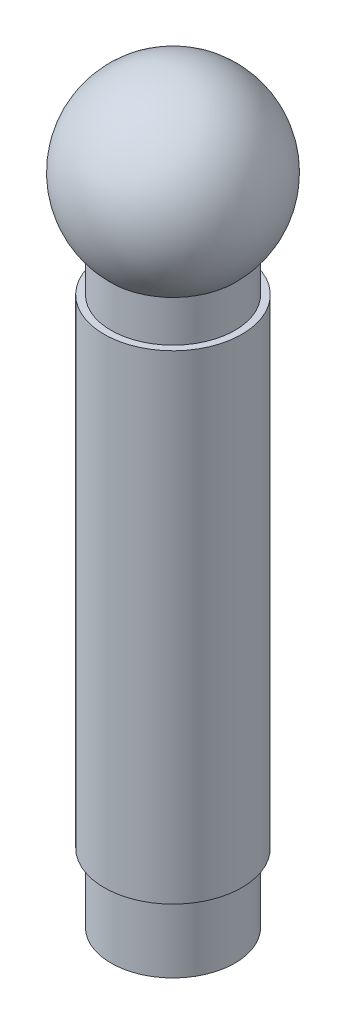
SolidWorks part; units mm, degrees
ref_plane "Front Plane" through (0, 0, 0) normal (0, 0, 1) x (1, 0, 0)
ref_plane "Top Plane" through (0, 0, 0) normal (0, 1, 0) x (1, 0, 0)
ref_plane "Right Plane" through (0, 0, 0) normal (1, 0, 0) x (0, 0, -1)
sketch "Sketch1" plane through (0, 0, 0) normal (0, 0, 1) x (1, 0, 0)
  line L0 (0, -29.8745) -> (0, 43.9331) construction
  line L1 (4.5, -75.1197) -> (4.5, -78.1197)
  line L2 (4.5, -78.1197) -> (5, -78.1197)
  line L3 (5, -78.1197) -> (5, -112.9293)
  line L4 (4.5, -117.9293) -> (0, -117.9293)
  line L5 (5, -112.9293) -> (4.5, -112.9293)
  line L6 (4.5, -112.9293) -> (4.5, -117.9293)
  line L7 (0, -117.9293) -> (0, -63.9293)
  arc A0 (4.5, -75.1197) -> (0, -63.9293) centre (0, -70.4293) ccw
  dimension "D1" = 6.5
  dimension "D2" = 54
  dimension "D3" = 5
  dimension "D4" = 0.5
  dimension "D5" = 3
  dimension "D6" = 0.5
  dimension "D7" = 5
revolve "Revolve1" add sketch "Sketch1" angle 360 about L0
sketch "Sketch2" plane through (0, -117.9293, 0) normal (0, -1, 0) x (-1, 0, 0)
  line L0 (2.5, -1) -> (-2.5, 1) construction
  line L1 (2.5, -1) -> (-2.5, -1)
  line L2 (2.5, -1) -> (2.5, 1)
  line L3 (2.5, 1) -> (-2.5, 1)
  line L4 (-2.5, -1) -> (-2.5, 1)
  point P5 (0, 0)
  dimension "D1" = 5
  dimension "D2" = 2
extrude "Cut-Extrude1" cut sketch "Sketch2" against normal blind 10
